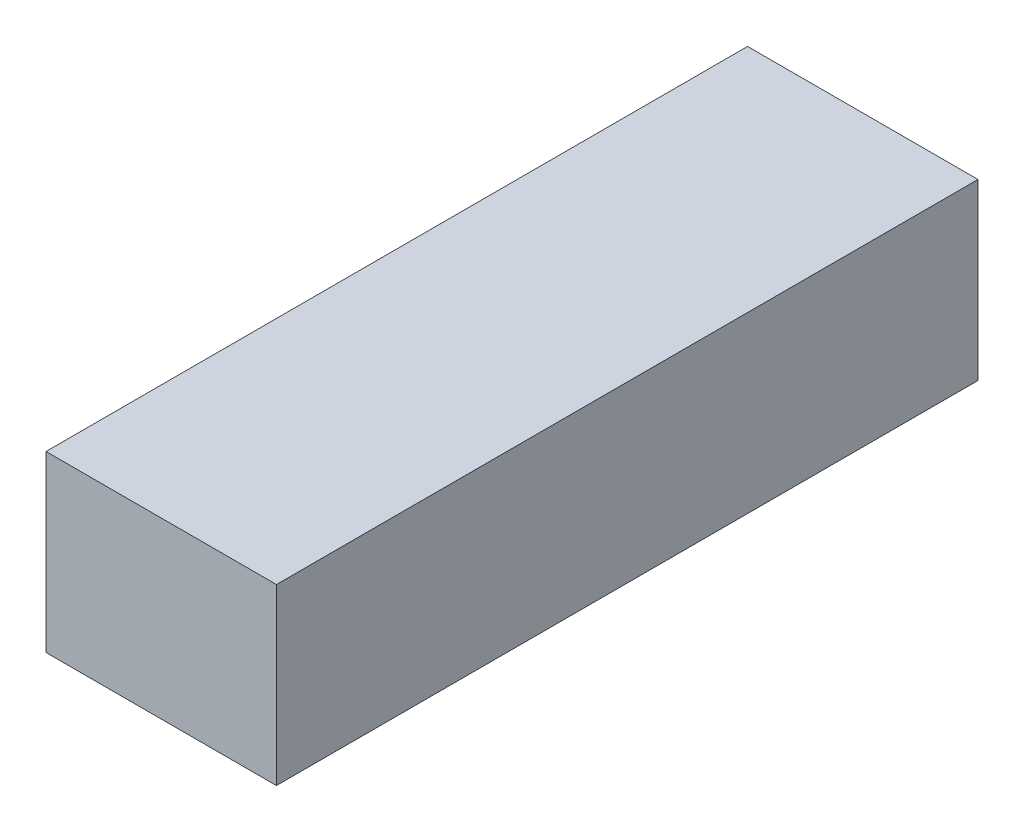
SolidWorks part; units mm, degrees
ref_plane "Front Plane" through (0, 0, 0) normal (0, 0, 1) x (1, 0, 0)
ref_plane "Top Plane" through (0, 0, 0) normal (0, 1, 0) x (1, 0, 0)
ref_plane "Right Plane" through (0, 0, 0) normal (1, 0, 0) x (0, 0, -1)
sketch "Sketch1" plane through (0, 0, 0) normal (0, 0, 1) x (1, 0, 0)
  line L1 (-22.5, -17) -> (22.5, -17)
  line L2 (-22.5, -17) -> (-22.5, 17)
  line L3 (-22.5, 17) -> (22.5, 17)
  line L4 (22.5, -17) -> (22.5, 17)
  line L5 (-22.5, -17) -> (22.5, 17) construction
  line L6 (-22.5, 17) -> (22.5, -17) construction
  point P0 (0, 0)
  dimension "D1" = 45
  dimension "D2" = 34
extrude "Boss-Extrude1" add sketch "Sketch1" along normal blind 137
